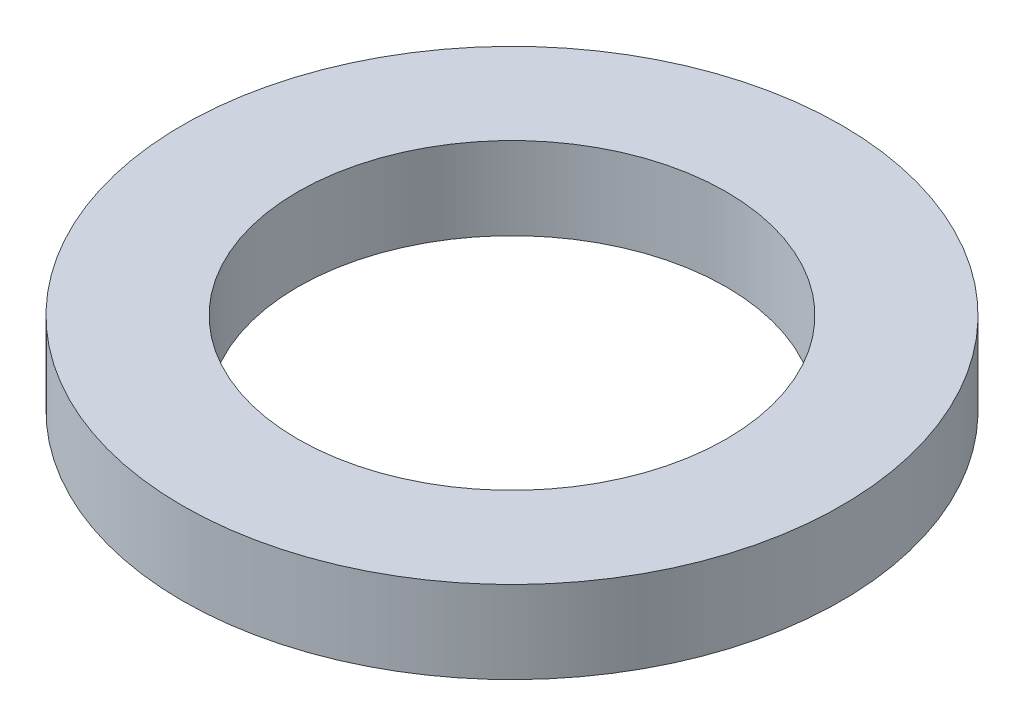
SolidWorks part; units mm, degrees
ref_plane "Front Plane" through (0, 0, 0) normal (0, 0, 1) x (1, 0, 0)
ref_plane "Top Plane" through (0, 0, 0) normal (0, 1, 0) x (1, 0, 0)
ref_plane "Right Plane" through (0, 0, 0) normal (1, 0, 0) x (0, 0, -1)
sketch "Sketch1" plane through (0, 0, 0) normal (0, 1, 0) x (1, 0, 0)
  circle A0 centre (0, 0) radius 2.6
  circle A1 centre (0, 0) radius 4
  dimension "D1" = 5.2
  dimension "D2" = 8
extrude "Boss-Extrude1" add sketch "Sketch1" along normal blind 1
